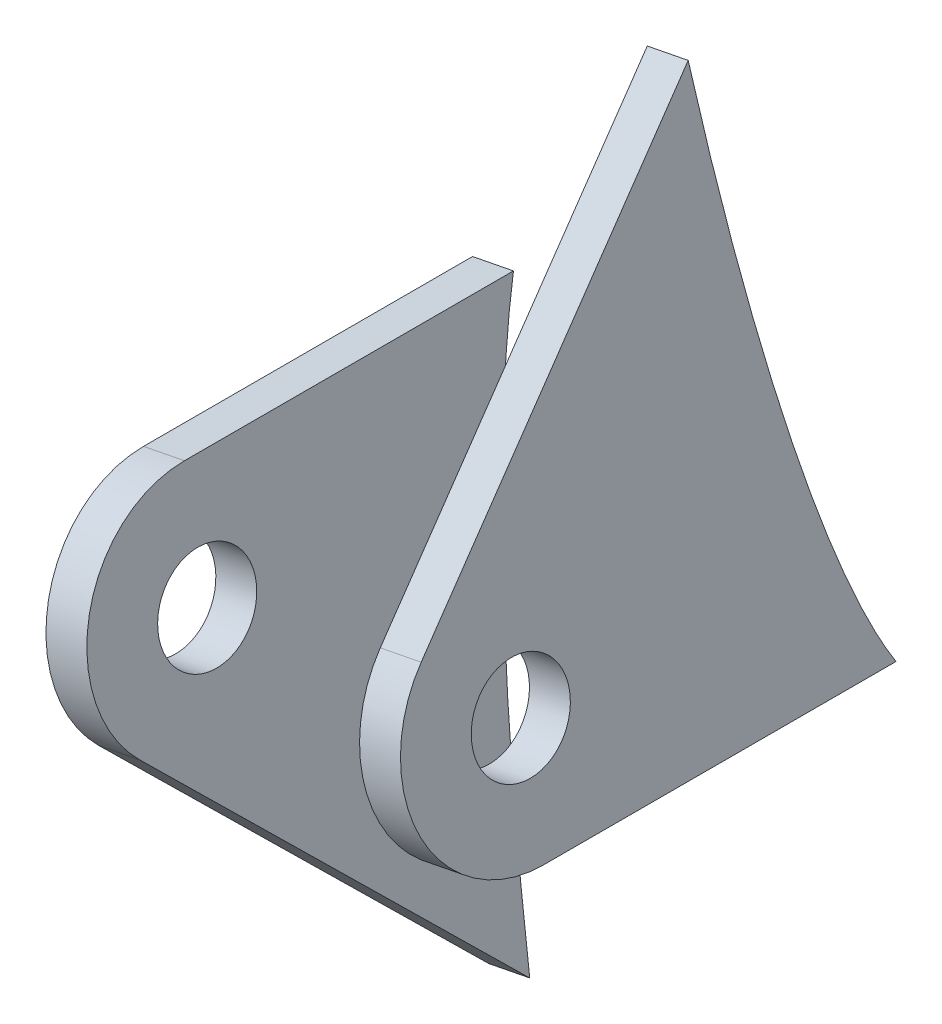
SolidWorks part; units mm, degrees
material "1.0545 (S355N)"
ref_plane "Płaszczyzna XY" through (0, 0, 0) normal (0, 0, 1) x (1, 0, 0)
ref_plane "Płaszczyzna XZ" through (0, 0, 0) normal (0, 1, 0) x (1, 0, 0)
ref_plane "Płaszczyzna YZ" through (0, 0, 0) normal (1, 0, 0) x (0, 0, -1)
ref_plane "Płaszczyzna1" through (1360.6279, 266.5539, 0.4526) normal (-0.9813, -0.1923, -0.0003) x (-0.0003, -0.0001, 1)
sketch "Szkic1" plane through (1360.6279, 266.5539, 0.4526) normal (-0.9813, -0.1923, -0.0003) x (-0.0003, -0.0001, 1)
  line L0 (433.9924, -370.9418) -> (408.6407, -370.9418)
  line L1 (440.0028, -356.4314) -> (416.2291, -332.6577)
  line L2 (417.7425, -381.3826) -> (417.7425, -278.4768) construction
  circle A0 centre (433.9924, -362.4418) radius 3.5
  arc A1 (433.9924, -370.9418) -> (440.0028, -356.4314) centre (433.9924, -362.4418) ccw
  circle A2 centre (433.9924, -362.4418) radius 8.5 construction
  spline S1 degree 3 poles (404.5432, -244.4813) (429.5432, -244.4797) (429.5515, -374.5183) (404.5515, -374.5199) (379.5515, -374.5215) (379.5432, -244.4829) (404.5432, -244.4813) (429.5432, -244.4797) (429.5515, -374.5183) knots -0.5 0 0 0 0.5 0.5 0.5 1 1 1 1.5 1.5 1.5 weights 1 0.333333 0.333333 1 0.333333 0.333333 1 0.333333 0.333333 only from (404.5432, -244.4813) to (404.5432, -244.4813)
  dimension "D1" = 7
  dimension "D3" = 45
  dimension "D4" = 90
  dimension "D2" = 5
extrude "Dodanie-wyciągnięcie1" add sketch "Szkic1" against normal blind 3 contours L1 S1 L0 A1 A0
ref_plane "Płaszczyzna3" through (1341.001, 262.7089, 0.4461) normal (0.9813, 0.1923, 0.0003) x (0.0003, 0.0001, -1)
sketch "Szkic2" plane through (1341.001, 262.7089, 0.4461) normal (0.9813, 0.1923, 0.0003) x (0.0003, 0.0001, -1)
  line L0 (-447.1301, -382.2563) -> (-447.1301, -307.4901) construction
  line L1 (-440.0028, -368.4522) -> (-416.4708, -391.9841)
  line L2 (-433.9924, -353.9418) -> (-410.331, -353.9418)
  circle A0 centre (-433.9924, -362.4418) radius 3.5
  circle A1 centre (-433.9924, -362.4418) radius 3.5 construction
  arc A2 (-433.9924, -353.9418) -> (-440.0028, -368.4522) centre (-433.9924, -362.4418) ccw
  circle A3 centre (-433.9924, -362.4418) radius 8.5 construction
  spline S1 degree 3 poles (-413.5673, -456.6554) (-422.4917, -408.3599) (-417.4529, -346.6925) (-404.5724, -346.5717) (-391.692, -346.4509) (-386.6181, -408.0234) (-395.5149, -456.4861) knots 0 0 0 0 0.5 0.5 0.5 1 1 1 1 weights 1 0.59504 0.59504 1 0.59504 0.59504 1
  dimension "D1" = 5
  dimension "D2" = 45
extrude "Dodanie-wyciągnięcie2" add sketch "Szkic2" against normal blind 3 separate body contours L1 S1 L2 A2 A0
